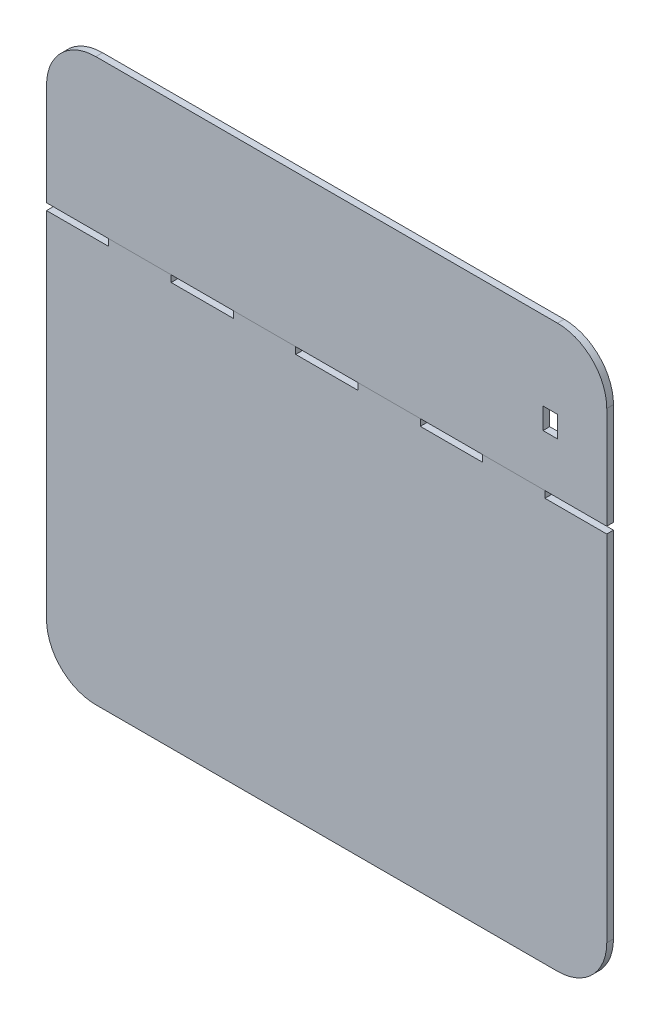
SolidWorks part; units mm, degrees
material "Pine"
ref_plane "Front Plane" through (0, 0, 0) normal (0, 0, 1) x (1, 0, 0)
ref_plane "Top Plane" through (0, 0, 0) normal (0, 1, 0) x (1, 0, 0)
ref_plane "Right Plane" through (0, 0, 0) normal (1, 0, 0) x (0, 0, -1)
sketch "Sketch1" plane through (0, 0, 0) normal (0, 0, 1) x (1, 0, 0)
  line L1 (0, 0) -> (500, 0)
  line L2 (0, 0) -> (0, 501)
  line L3 (0, 501) -> (500, 501)
  line L4 (500, 0) -> (500, 501)
  dimension "D1" = 500
  dimension "D2" = 501
extrude "Boss-Extrude1" add sketch "Sketch1" along normal blind 6
fillet "Fillet1" radius 44 4 edges at (0, 0, 3) (0, 501, 3) (500, 0, 3) (500, 501, 3)
sketch "Sketch2" plane through (0, 0, 0) normal (0, 0, -1) x (-1, 0, 0)
  line L0 (-456, 501) -> (-44, 501) construction
  line L1 (0, 360) -> (-55.5, 360)
  line L2 (0, 360) -> (0, 366)
  line L3 (0, 366) -> (-55.5, 366)
  line L4 (-55.5, 360) -> (-55.5, 366)
  line L5 (0, 457) -> (0, 44) construction
  dimension "D1" = 135
  dimension "D2" = 6
  dimension "D3" = 0
  dimension "D4" = 55.5
extrude "Cut-Extrude1" cut sketch "Sketch2" against normal blind 10
pattern_linear "LPattern1" count 5 spacing 111.2 along (1, 0, 0) of "Cut-Extrude1"
sketch "Sketch4" plane through (0, 0, 0) normal (0, 0, -1) x (-1, 0, 0)
  line L0 (-456, 501) -> (-44, 501) construction
  line L1 (-456, 430.5) -> (-443.1, 430.5)
  line L2 (-456, 430.5) -> (-456, 411.5)
  line L3 (-456, 411.5) -> (-443.1, 411.5)
  line L4 (-443.1, 430.5) -> (-443.1, 411.5)
  point P5 (-443.1, 421)
  dimension "D1" = 19
  dimension "D2" = 12.9
  dimension "D3" = 0
  dimension "D4" = 80
extrude "Cut-Extrude3" cut sketch "Sketch4" against normal blind 10
sketch "Sketch3" plane through (0, 0, 0) normal (0, 0, -1) x (-1, 0, 0)
  line L0 (-456, 411.5) -> (-443.1, 411.5) construction
  circle A0 centre (-449.55, 401.5) radius 2.5
  point P6 (-449.55, 411.5)
  dimension "D1" = 0
  dimension "D3" = 5
  dimension "D2" = 10
sketch "Sketch5" plane through (0, 0, 6) normal (0, 0, 1) x (1, 0, 0)
  line L0 (0, 366) -> (500, 366)
  line L1 (0, 366) -> (55.5, 366) construction
  line L2 (444.8, 366) -> (500, 366) construction
split "Split1" trim tools "Sketch5" bodies to split 105 resulting bodies 106 107
